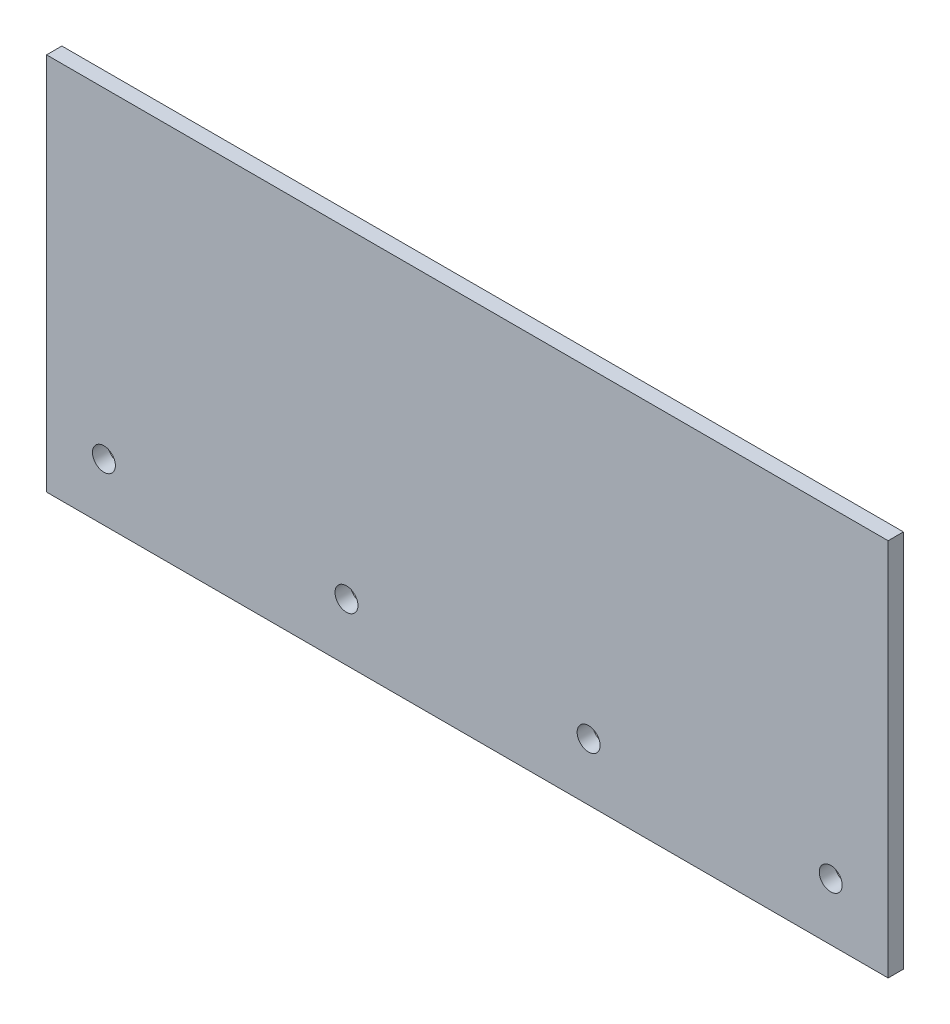
SolidWorks part; units mm, degrees
ref_plane "Přední rovina" through (0, 0, 0) normal (0, 0, 1) x (1, 0, 0)
ref_plane "Horní rovina" through (0, 0, 0) normal (0, 1, 0) x (1, 0, 0)
ref_plane "Pravá rovina" through (0, 0, 0) normal (1, 0, 0) x (0, 0, -1)
sketch "Skica1" plane through (0, 0, 0) normal (0, 0, 1) x (1, 0, 0)
  line L0 (220, 15) -> (0, 15) construction
  line L3 (0, 99) -> (220, 99)
  line L5 (0, 0) -> (220, 0)
  line L6 (0, 99) -> (0, 0)
  line L8 (220, 0) -> (220, 99)
  line L11 (110, 99) -> (110, -101) construction
  circle A0 centre (205, 15) radius 3
  circle A1 centre (15, 15) radius 3
  circle A2 centre (141.7, 15) radius 3
  circle A3 centre (78.4, 15) radius 3
  dimension "D3" = 6
  dimension "D9" = 63.4
  dimension "D1" = 220
  dimension "D2" = 15
  dimension "D4" = 99
  dimension "D5" = 15
  dimension "D6" = 15
  dimension "D7" = 63.3
  dimension "D8" = 63.3
extrude "Přidat vysunutím1" add sketch "Skica1" along normal blind 4
